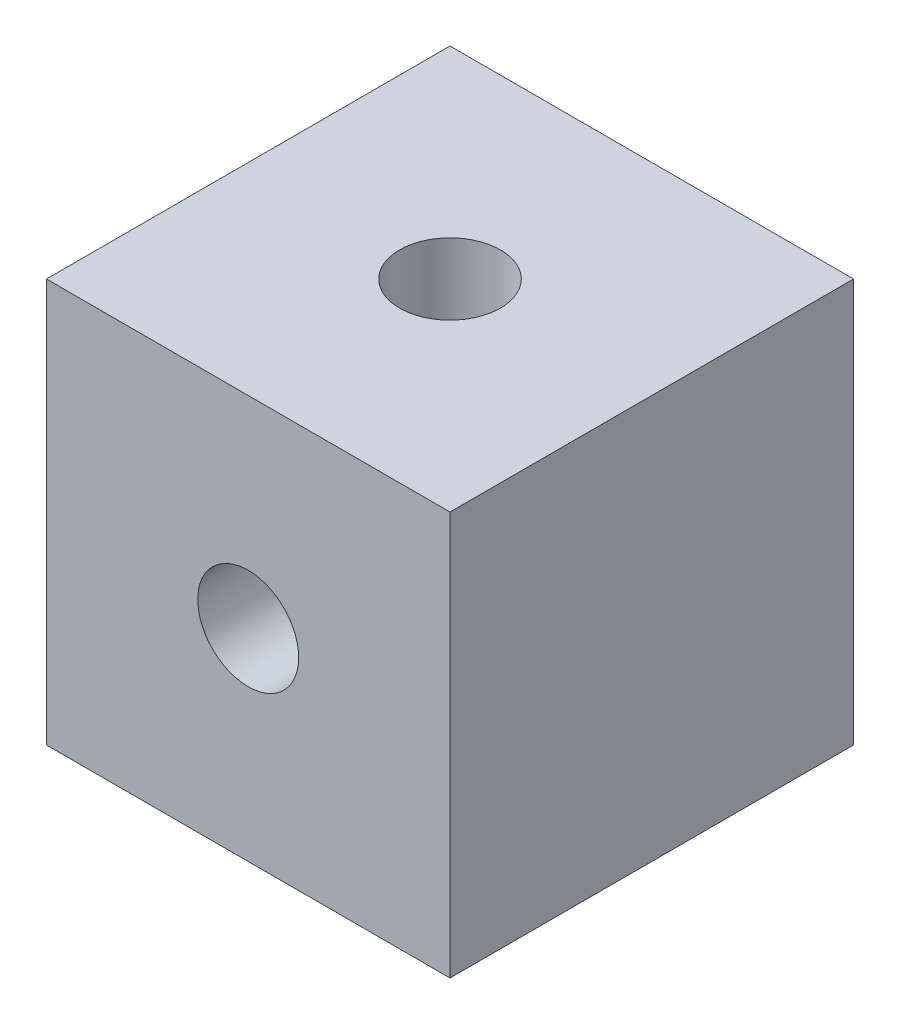
SolidWorks part; units mm, degrees
ref_plane "Front Plane" through (0, 0, 0) normal (0, 0, 1) x (1, 0, 0)
ref_plane "Top Plane" through (0, 0, 0) normal (0, 1, 0) x (1, 0, 0)
ref_plane "Right Plane" through (0, 0, 0) normal (1, 0, 0) x (0, 0, -1)
sketch "Sketch1" plane through (0, 0, 0) normal (0, 0, 1) x (1, 0, 0)
  line L1 (12.7, -12.7) -> (-12.7, -12.7)
  line L2 (12.7, -12.7) -> (12.7, 12.7)
  line L3 (12.7, 12.7) -> (-12.7, 12.7)
  line L4 (-12.7, -12.7) -> (-12.7, 12.7)
  line L5 (12.7, -12.7) -> (-12.7, 12.7) construction
  line L6 (12.7, 12.7) -> (-12.7, -12.7) construction
  point P0 (0, 0)
  dimension "D1" = 25.4
  dimension "D2" = 25.4
extrude "Boss-Extrude1" add sketch "Sketch1" along normal blind 25.4
sketch "Sketch2" plane through (0, 0, 25.4) normal (0, 0, 1) x (1, 0, 0)
  circle A0 centre (0, 0) radius 3.175
extrude "Cut-Extrude1" cut sketch "Sketch2" against normal blind 12.7
sketch "Sketch3" plane through (0, 12.7, 0) normal (0, 1, 0) x (1, 0, 0)
  line L0 (0, 0) -> (0, -25.4) construction
  line L1 (12.7, 0) -> (-12.7, 0) construction
  line L2 (12.7, -25.4) -> (-12.7, -25.4) construction
  line L3 (-12.7, -12.7) -> (12.7, -12.7) construction
  line L4 (-12.7, -25.4) -> (-12.7, 0) construction
  line L5 (12.7, -25.4) -> (12.7, 0) construction
  circle A0 centre (0, -12.7) radius 3.175
extrude "Cut-Extrude2" cut sketch "Sketch3" against normal blind 12.7
